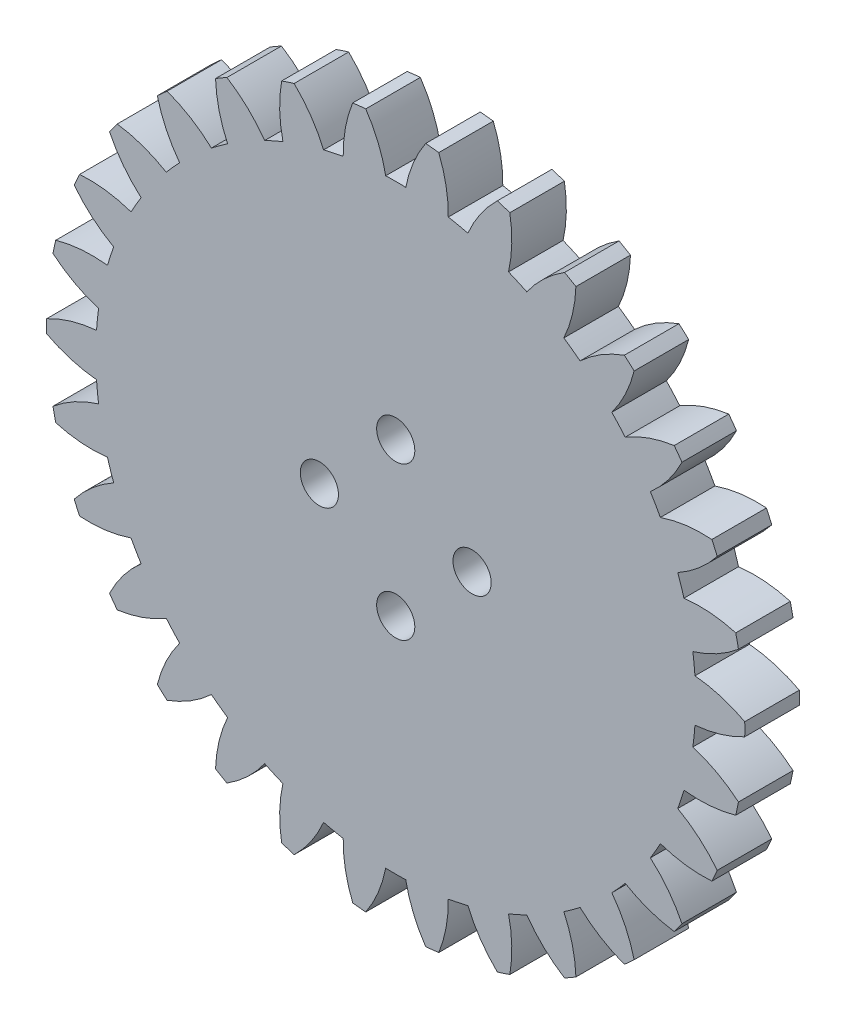
SolidWorks part; units mm, degrees
ref_plane "前视基准面" through (0, 0, 0) normal (0, 0, 1) x (1, 0, 0)
ref_plane "上视基准面" through (0, 0, 0) normal (0, 1, 0) x (1, 0, 0)
ref_plane "右视基准面" through (0, 0, 0) normal (1, 0, 0) x (0, 0, -1)
sketch "草图1" plane through (0, 0, 0) normal (0, 0, 1) x (1, 0, 0)
  arc A0 (-31.9943, -0.6021) -> (-27.4291, -1.9593) centre (-26.3602, 9.993) ccw
  arc A1 (-27.4291, -1.9593) -> (-27.2371, -3.7863) centre (0, 0) ccw
  arc A2 (-27.2371, -3.7863) -> (-31.4204, -6.063) centre (-23.7065, -15.2552) ccw
  arc A3 (-31.4204, -6.063) -> (-31.17, -7.241) centre (0, 0) ccw
  arc A4 (-31.17, -7.241) -> (-26.4224, -7.6193) centre (-27.8618, 4.294) ccw
  arc A5 (-26.4224, -7.6193) -> (-25.8547, -9.3665) centre (0, 0) ccw
  arc A6 (-25.8547, -9.3665) -> (-29.4732, -12.4632) centre (-20.0167, -19.8507) ccw
  arc A7 (-29.4732, -12.4632) -> (-28.9834, -13.5633) centre (0, 0) ccw
  arc A8 (-28.9834, -13.5633) -> (-24.2608, -12.9463) centre (-28.1458, -1.5926) ccw
  arc A9 (-24.2608, -12.9463) -> (-23.3423, -14.5373) centre (0, 0) ccw
  arc A10 (-23.3423, -14.5373) -> (-26.2379, -18.3187) centre (-15.4521, -23.5786) ccw
  arc A11 (-26.2379, -18.3187) -> (-25.53, -19.2929) centre (0, 0) ccw
  arc A12 (-25.53, -19.2929) -> (-21.039, -17.7075) centre (-27.1996, -7.4096) ccw
  arc A13 (-21.039, -17.7075) -> (-19.8097, -19.0728) centre (0, 0) ccw
  arc A14 (-19.8097, -19.0728) -> (-21.8559, -23.3735) centre (-10.2122, -26.2761) ccw
  arc A15 (-21.8559, -23.3735) -> (-20.9609, -24.1793) centre (0, 0) ccw
  arc A16 (-20.9609, -24.1793) -> (-16.8976, -21.6948) centre (-25.0647, -12.9028) ccw
  arc A17 (-16.8976, -21.6948) -> (-15.4114, -22.7747) centre (0, 0) ccw
  arc A18 (-15.4114, -22.7747) -> (-16.5186, -27.4068) centre (-4.5259, -27.8251) ccw
  arc A19 (-16.5186, -27.4068) -> (-15.4757, -28.009) centre (0, 0) ccw
  arc A20 (-15.4757, -28.009) -> (-12.0177, -24.734) centre (-21.8343, -17.8321) ccw
  arc A21 (-12.0177, -24.734) -> (-10.3395, -25.4812) centre (0, 0) ccw
  arc A22 (-10.3395, -25.4812) -> (-10.4594, -30.2424) centre (1.3582, -28.158) ccw
  arc A23 (-10.4594, -30.2424) -> (-9.3141, -30.6145) centre (0, 0) ccw
  arc A24 (-9.3141, -30.6145) -> (-6.6127, -26.6921) centre (-17.6497, -21.982) ccw
  arc A25 (-6.6127, -26.6921) -> (-4.8157, -27.074) centre (0, 0) ccw
  arc A26 (-4.8157, -27.074) -> (-3.9431, -31.7561) centre (7.1829, -27.2603) ccw
  arc A27 (-3.9431, -31.7561) -> (-2.7455, -31.882) centre (0, 0) ccw
  arc A28 (-2.7455, -31.882) -> (-0.9186, -27.4837) centre (-12.6936, -25.1712) ccw
  arc A29 (-0.9186, -27.4837) -> (0.9186, -27.4837) centre (0, 0) ccw
  arc A30 (0.9186, -27.4837) -> (2.7455, -31.882) centre (12.6936, -25.1712) ccw
  arc A31 (2.7455, -31.882) -> (3.9431, -31.7561) centre (0, 0) ccw
  arc A32 (3.9431, -31.7561) -> (4.8157, -27.074) centre (-7.1829, -27.2603) ccw
  arc A33 (4.8157, -27.074) -> (6.6127, -26.6921) centre (0, 0) ccw
  arc A34 (6.6127, -26.6921) -> (9.3141, -30.6145) centre (17.6497, -21.982) ccw
  arc A35 (9.3141, -30.6145) -> (10.4594, -30.2424) centre (0, 0) ccw
  arc A36 (10.4594, -30.2424) -> (10.3395, -25.4812) centre (-1.3582, -28.158) ccw
  arc A37 (10.3395, -25.4812) -> (12.0177, -24.734) centre (0, 0) ccw
  arc A38 (12.0177, -24.734) -> (15.4757, -28.009) centre (21.8343, -17.8321) ccw
  arc A39 (15.4757, -28.009) -> (16.5186, -27.4068) centre (0, 0) ccw
  arc A40 (16.5186, -27.4068) -> (15.4114, -22.7747) centre (4.5259, -27.8251) ccw
  arc A41 (15.4114, -22.7747) -> (16.8976, -21.6948) centre (0, 0) ccw
  arc A42 (16.8976, -21.6948) -> (20.9609, -24.1793) centre (25.0647, -12.9028) ccw
  arc A43 (20.9609, -24.1793) -> (21.8559, -23.3735) centre (0, 0) ccw
  arc A44 (21.8559, -23.3735) -> (19.8097, -19.0728) centre (10.2122, -26.2761) ccw
  arc A45 (19.8097, -19.0728) -> (21.039, -17.7075) centre (0, 0) ccw
  arc A46 (21.039, -17.7075) -> (25.53, -19.2929) centre (27.1996, -7.4096) ccw
  arc A47 (25.53, -19.2929) -> (26.2379, -18.3187) centre (0, 0) ccw
  arc A48 (26.2379, -18.3187) -> (23.3423, -14.5373) centre (15.4521, -23.5786) ccw
  arc A49 (23.3423, -14.5373) -> (24.2608, -12.9463) centre (0, 0) ccw
  arc A50 (24.2608, -12.9463) -> (28.9834, -13.5633) centre (28.1458, -1.5926) ccw
  arc A51 (28.9834, -13.5633) -> (29.4732, -12.4632) centre (0, 0) ccw
  arc A52 (29.4732, -12.4632) -> (25.8547, -9.3665) centre (20.0167, -19.8507) ccw
  arc A53 (25.8547, -9.3665) -> (26.4224, -7.6193) centre (0, 0) ccw
  arc A54 (26.4224, -7.6193) -> (31.17, -7.241) centre (27.8618, 4.294) ccw
  arc A55 (31.17, -7.241) -> (31.4204, -6.063) centre (0, 0) ccw
  arc A56 (31.4204, -6.063) -> (27.2371, -3.7863) centre (23.7065, -15.2552) ccw
  arc A57 (27.2371, -3.7863) -> (27.4291, -1.9593) centre (0, 0) ccw
  arc A58 (27.4291, -1.9593) -> (31.9943, -0.6021) centre (26.3602, 9.993) ccw
  arc A59 (31.9943, -0.6021) -> (31.9943, 0.6021) centre (0, 0) ccw
  arc A60 (31.9943, 0.6021) -> (27.4291, 1.9593) centre (26.3602, -9.993) ccw
  arc A61 (27.4291, 1.9593) -> (27.2371, 3.7863) centre (0, 0) ccw
  arc A62 (27.2371, 3.7863) -> (31.4204, 6.063) centre (23.7065, 15.2552) ccw
  arc A63 (31.4204, 6.063) -> (31.17, 7.241) centre (0, 0) ccw
  arc A64 (31.17, 7.241) -> (26.4224, 7.6193) centre (27.8618, -4.294) ccw
  arc A65 (26.4224, 7.6193) -> (25.8547, 9.3665) centre (0, 0) ccw
  arc A66 (25.8547, 9.3665) -> (29.4732, 12.4632) centre (20.0167, 19.8507) ccw
  arc A67 (29.4732, 12.4632) -> (28.9834, 13.5633) centre (0, 0) ccw
  arc A68 (28.9834, 13.5633) -> (24.2608, 12.9463) centre (28.1458, 1.5926) ccw
  arc A69 (24.2608, 12.9463) -> (23.3423, 14.5373) centre (0, 0) ccw
  arc A70 (23.3423, 14.5373) -> (26.2379, 18.3187) centre (15.4521, 23.5786) ccw
  arc A71 (26.2379, 18.3187) -> (25.53, 19.2929) centre (0, 0) ccw
  arc A72 (25.53, 19.2929) -> (21.039, 17.7075) centre (27.1996, 7.4096) ccw
  arc A73 (21.039, 17.7075) -> (19.8097, 19.0728) centre (0, 0) ccw
  arc A74 (19.8097, 19.0728) -> (21.8559, 23.3735) centre (10.2122, 26.2761) ccw
  arc A75 (21.8559, 23.3735) -> (20.9609, 24.1793) centre (0, 0) ccw
  arc A76 (20.9609, 24.1793) -> (16.8976, 21.6948) centre (25.0647, 12.9028) ccw
  arc A77 (16.8976, 21.6948) -> (15.4114, 22.7747) centre (0, 0) ccw
  arc A78 (15.4114, 22.7747) -> (16.5186, 27.4068) centre (4.5259, 27.8251) ccw
  arc A79 (16.5186, 27.4068) -> (15.4757, 28.009) centre (0, 0) ccw
  arc A80 (15.4757, 28.009) -> (12.0177, 24.734) centre (21.8343, 17.8321) ccw
  arc A81 (12.0177, 24.734) -> (10.3395, 25.4812) centre (0, 0) ccw
  arc A82 (10.3395, 25.4812) -> (10.4594, 30.2424) centre (-1.3582, 28.158) ccw
  arc A83 (10.4594, 30.2424) -> (9.3141, 30.6145) centre (0, 0) ccw
  arc A84 (9.3141, 30.6145) -> (6.6127, 26.6921) centre (17.6497, 21.982) ccw
  arc A85 (6.6127, 26.6921) -> (4.8157, 27.074) centre (0, 0) ccw
  arc A86 (4.8157, 27.074) -> (3.9431, 31.7561) centre (-7.1829, 27.2603) ccw
  arc A87 (3.9431, 31.7561) -> (2.7455, 31.882) centre (0, 0) ccw
  arc A88 (2.7455, 31.882) -> (0.9186, 27.4837) centre (12.6936, 25.1712) ccw
  arc A89 (0.9186, 27.4837) -> (-0.9186, 27.4837) centre (0, 0) ccw
  arc A90 (-0.9186, 27.4837) -> (-2.7455, 31.882) centre (-12.6936, 25.1712) ccw
  arc A91 (-2.7455, 31.882) -> (-3.9431, 31.7561) centre (0, 0) ccw
  arc A92 (-3.9431, 31.7561) -> (-4.8157, 27.074) centre (7.1829, 27.2603) ccw
  arc A93 (-4.8157, 27.074) -> (-6.6127, 26.6921) centre (0, 0) ccw
  arc A94 (-6.6127, 26.6921) -> (-9.3141, 30.6145) centre (-17.6497, 21.982) ccw
  arc A95 (-9.3141, 30.6145) -> (-10.4594, 30.2424) centre (0, 0) ccw
  arc A96 (-10.4594, 30.2424) -> (-10.3395, 25.4812) centre (1.3582, 28.158) ccw
  arc A97 (-10.3395, 25.4812) -> (-12.0177, 24.734) centre (0, 0) ccw
  arc A98 (-12.0177, 24.734) -> (-15.4757, 28.009) centre (-21.8343, 17.8321) ccw
  arc A99 (-15.4757, 28.009) -> (-16.5186, 27.4068) centre (0, 0) ccw
  arc A100 (-16.5186, 27.4068) -> (-15.4114, 22.7747) centre (-4.5259, 27.8251) ccw
  arc A101 (-15.4114, 22.7747) -> (-16.8976, 21.6948) centre (0, 0) ccw
  arc A102 (-16.8976, 21.6948) -> (-20.9609, 24.1793) centre (-25.0647, 12.9028) ccw
  arc A103 (-20.9609, 24.1793) -> (-21.8559, 23.3735) centre (0, 0) ccw
  arc A104 (-21.8559, 23.3735) -> (-19.8097, 19.0728) centre (-10.2122, 26.2761) ccw
  arc A105 (-19.8097, 19.0728) -> (-21.039, 17.7075) centre (0, 0) ccw
  arc A106 (-21.039, 17.7075) -> (-25.53, 19.2929) centre (-27.1996, 7.4096) ccw
  arc A107 (-25.53, 19.2929) -> (-26.2379, 18.3187) centre (0, 0) ccw
  arc A108 (-26.2379, 18.3187) -> (-23.3423, 14.5373) centre (-15.4521, 23.5786) ccw
  arc A109 (-23.3423, 14.5373) -> (-24.2608, 12.9463) centre (0, 0) ccw
  arc A110 (-24.2608, 12.9463) -> (-28.9834, 13.5633) centre (-28.1458, 1.5926) ccw
  arc A111 (-28.9834, 13.5633) -> (-29.4732, 12.4632) centre (0, 0) ccw
  arc A112 (-29.4732, 12.4632) -> (-25.8547, 9.3665) centre (-20.0167, 19.8507) ccw
  arc A113 (-25.8547, 9.3665) -> (-26.4224, 7.6193) centre (0, 0) ccw
  arc A114 (-26.4224, 7.6193) -> (-31.17, 7.241) centre (-27.8618, -4.294) ccw
  arc A115 (-31.17, 7.241) -> (-31.4204, 6.063) centre (0, 0) ccw
  arc A116 (-31.4204, 6.063) -> (-27.2371, 3.7863) centre (-23.7065, 15.2552) ccw
  arc A117 (-27.2371, 3.7863) -> (-27.4291, 1.9593) centre (0, 0) ccw
  arc A118 (-27.4291, 1.9593) -> (-31.9943, 0.6021) centre (-26.3602, -9.993) ccw
  arc A119 (-31.9943, 0.6021) -> (-31.9943, -0.6021) centre (0, 0) ccw
extrude "凸台-拉伸1" add sketch "草图1" along normal blind 5
sketch "草图2" plane through (0, 0, 5) normal (0, 0, 1) x (1, 0, 0)
  circle A0 centre (0, 0) radius 7 construction
  circle A1 centre (0, 7) radius 1.75
  circle A2 centre (7, 0) radius 1.75
  circle A3 centre (0, -7) radius 1.75
  circle A4 centre (-7, 0) radius 1.75
  point P14 (0, 0)
  dimension "D1" = 14
  dimension "D2" = 3.5
  dimension "D3" = 4
extrude "切除-拉伸1" cut sketch "草图2" against normal blind 10
